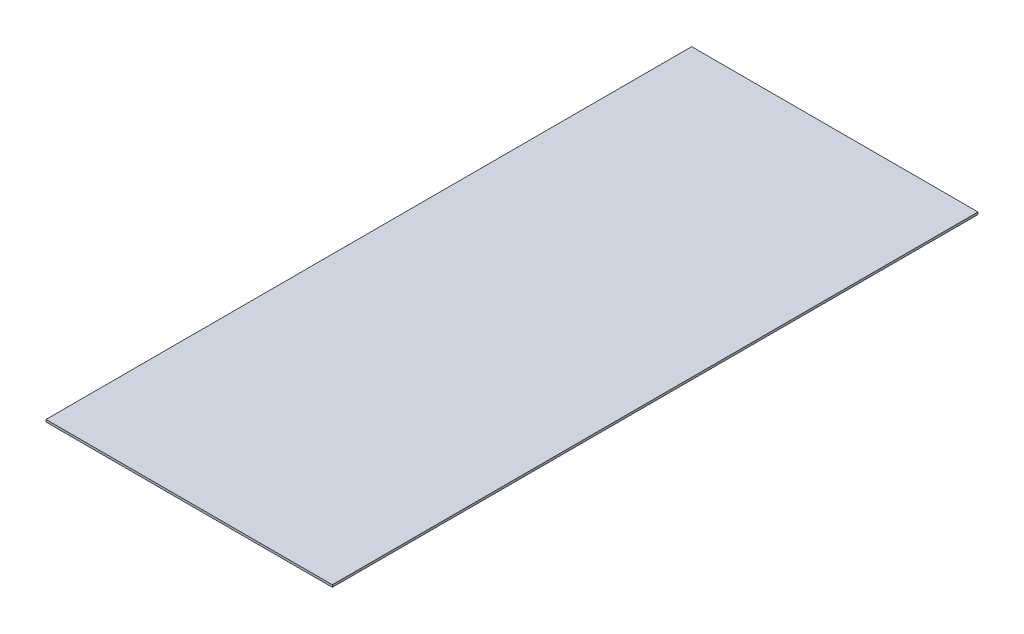
SolidWorks part; units mm, degrees
ref_plane "Front Plane" through (0, 0, 0) normal (0, 0, 1) x (1, 0, 0)
ref_plane "Top Plane" through (0, 0, 0) normal (0, 1, 0) x (1, 0, 0)
ref_plane "Right Plane" through (0, 0, 0) normal (1, 0, 0) x (0, 0, -1)
sketch "Sketch1" plane through (0, 0, 0) normal (0, 1, 0) x (1, 0, 0)
  line L1 (-161.925, 365.125) -> (161.925, 365.125)
  line L2 (-161.925, 365.125) -> (-161.925, -365.125)
  line L3 (-161.925, -365.125) -> (161.925, -365.125)
  line L4 (161.925, 365.125) -> (161.925, -365.125)
  line L5 (-161.925, 365.125) -> (161.925, -365.125) construction
  line L6 (-161.925, -365.125) -> (161.925, 365.125) construction
  point P0 (0, 0)
  dimension "D1" = 323.85
  dimension "D2" = 730.25
extrude "Boss-Extrude1" add sketch "Sketch1" along normal mid plane 2.54
